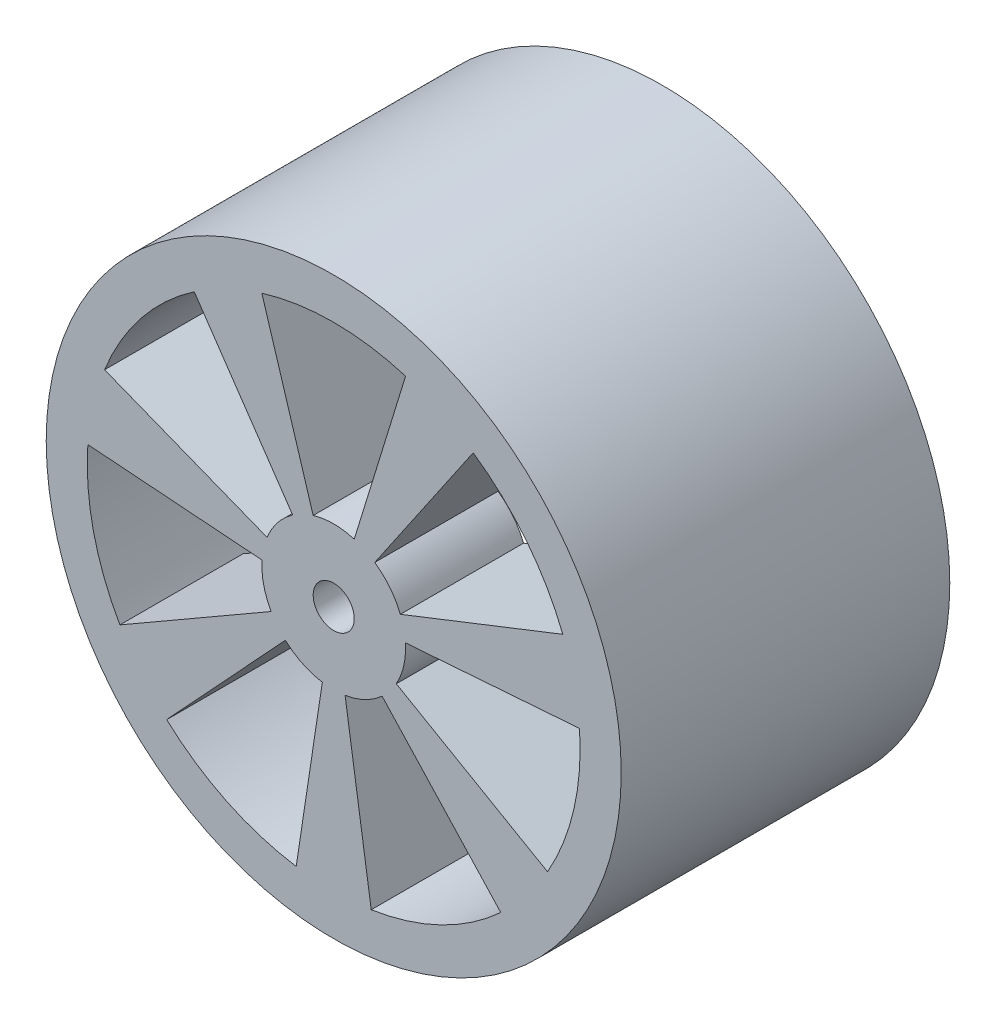
SolidWorks part; units mm, degrees
material "Nylon 101"
ref_plane "Front Plane" through (0, 0, 0) normal (0, 0, 1) x (1, 0, 0)
ref_plane "Top Plane" through (0, 0, 0) normal (0, 1, 0) x (1, 0, 0)
ref_plane "Right Plane" through (0, 0, 0) normal (1, 0, 0) x (0, 0, -1)
sketch "Sketch1" plane through (0, 0, 0) normal (0, 0, 1) x (1, 0, 0)
  circle A0 centre (0, 0) radius 28
  circle A1 centre (0, 0) radius 2
  dimension "D1" = 56
  dimension "D2" = 4
extrude "Boss-Extrude1" add sketch "Sketch1" along normal blind 32
sketch "Sketch2" plane through (0, 0, 0) normal (0, 0, -1) x (-1, 0, 0)
  circle A0 centre (0, 0) radius 24
  dimension "D1" = 48
extrude "Cut-Extrude1" cut sketch "Sketch2" against normal offset from surface (20 mm away) 12 up to face at (28, 0, 32)
sketch "Sketch3" plane through (0, 0, 20) normal (0, 0, -1) x (-1, 0, 0)
  line L1 (6, 0) -> (3, 5.1962)
  line L2 (3, 5.1962) -> (-3, 5.1962)
  line L3 (-3, 5.1962) -> (-6, 0)
  line L4 (-6, 0) -> (-3, -5.1962)
  line L5 (-3, -5.1962) -> (3, -5.1962)
  line L6 (3, -5.1962) -> (6, 0)
  circle A0 centre (0, 0) radius 6 construction
  dimension "D1" = 12
extrude "Cut-Extrude2" cut sketch "Sketch3" against normal blind 4
sketch "Sketch5" plane through (0, 0, 32) normal (0, 0, 1) x (1, 0, 0)
  line L0 (0, 7) -> (0, 24) construction
  line L1 (-7, 22.9565) -> (-2, 6.7082)
  line L2 (2, 6.7082) -> (7, 22.9565)
  line L3 (13.5837, 19.786) -> (3.9977, 5.7462)
  line L4 (6.4917, 2.6188) -> (22.3125, 8.8403)
  line L5 (23.9386, 1.7162) -> (6.9851, 0.4571)
  line L6 (6.095, -3.4426) -> (20.8233, -11.9328)
  line L7 (16.2672, -17.6459) -> (4.7125, -5.1761)
  line L8 (1.1086, -6.9117) -> (3.6537, -23.7203)
  line L9 (-3.6537, -23.7203) -> (-1.1086, -6.9117)
  line L10 (-4.7125, -5.1761) -> (-16.2672, -17.6459)
  line L11 (-20.8233, -11.9328) -> (-6.095, -3.4426)
  line L12 (-6.9851, 0.4571) -> (-23.9386, 1.7162)
  line L13 (-22.3125, 8.8403) -> (-6.4917, 2.6188)
  line L14 (-3.9977, 5.7462) -> (-13.5837, 19.786)
  arc A0 (-3.9977, 5.7462) -> (-6.4917, 2.6188) centre (0, 0) ccw
  arc A1 (-13.5837, 19.786) -> (-22.3125, 8.8403) centre (0, 0) ccw
  arc A2 (-7, 22.9565) -> (7, 22.9565) centre (0, 0) cw
  arc A3 (-2, 6.7082) -> (2, 6.7082) centre (0, 0) cw
  arc A4 (3.9977, 5.7462) -> (6.4917, 2.6188) centre (0, 0) cw
  arc A5 (13.5837, 19.786) -> (22.3125, 8.8403) centre (0, 0) cw
  arc A6 (6.9851, 0.4571) -> (6.095, -3.4426) centre (0, 0) cw
  arc A7 (23.9386, 1.7162) -> (20.8233, -11.9328) centre (0, 0) cw
  arc A8 (4.7125, -5.1761) -> (1.1086, -6.9117) centre (0, 0) cw
  arc A9 (16.2672, -17.6459) -> (3.6537, -23.7203) centre (0, 0) cw
  arc A10 (-1.1086, -6.9117) -> (-4.7125, -5.1761) centre (0, 0) cw
  arc A11 (-3.6537, -23.7203) -> (-16.2672, -17.6459) centre (0, 0) cw
  arc A12 (-6.095, -3.4426) -> (-6.9851, 0.4571) centre (0, 0) cw
  arc A13 (-20.8233, -11.9328) -> (-23.9386, 1.7162) centre (0, 0) cw
  arc A28 (-6.4917, 2.6188) -> (-3.9977, 5.7462) centre (0, 0) cw [skipped]
  arc A29 (-22.3125, 8.8403) -> (-13.5837, 19.786) centre (0, 0) cw [skipped]
  point P12 (7.6865, 22.7358)
  point P13 (6.9851, 22.955)
  point P36 (0, 0)
  dimension "D1" = 14
  dimension "D2" = 48
  dimension "D5" = 14
  dimension "D3" = 4
  dimension "D4" = 7
extrude "Cut-Extrude4" cut sketch "Sketch5" against normal through all
